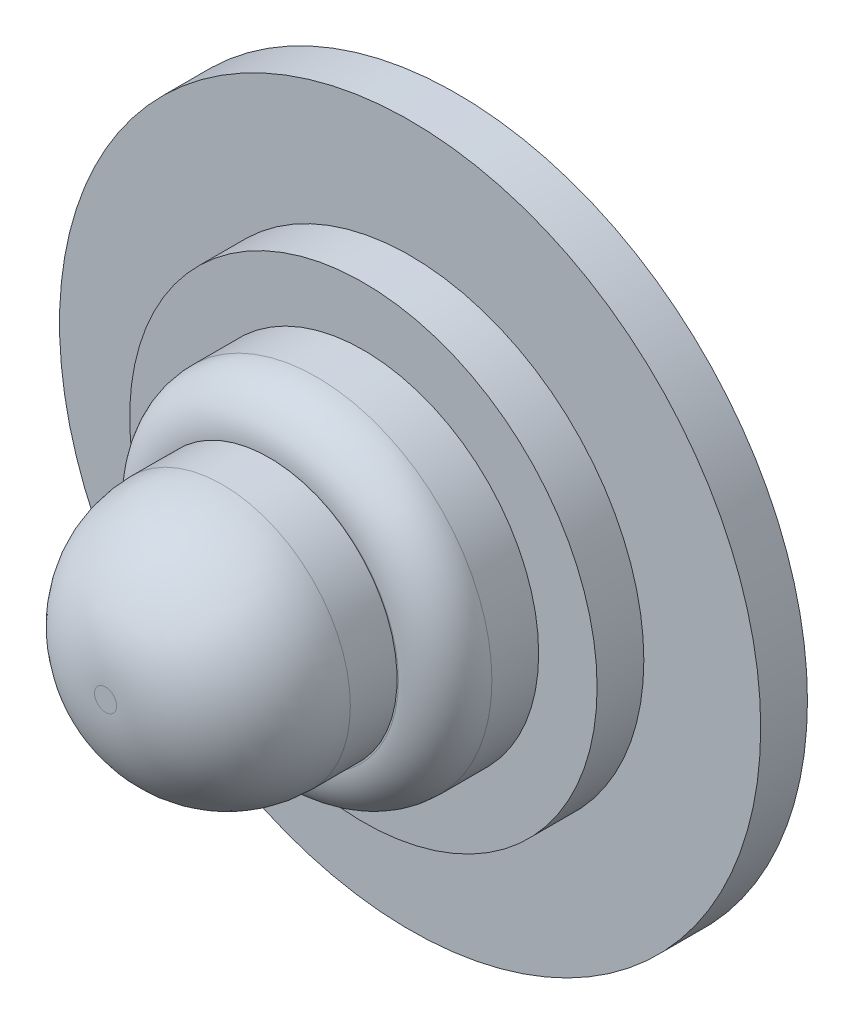
SolidWorks part; units mm, degrees
ref_plane "Front Plane" through (0, 0, 0) normal (0, 0, 1) x (1, 0, 0)
ref_plane "Top Plane" through (0, 0, 0) normal (0, 1, 0) x (1, 0, 0)
ref_plane "Right Plane" through (0, 0, 0) normal (1, 0, 0) x (0, 0, -1)
sketch "Sketch1" plane through (0, 0, 0) normal (0, 0, 1) x (1, 0, 0)
  circle A0 centre (-7.5327, 13.1274) radius 15
  dimension "D1" = 30
extrude "Boss-Extrude1" add sketch "Sketch1" along normal blind 2
sketch "Sketch2" plane through (0, 0, 2) normal (0, 0, 1) x (1, 0, 0)
  circle A0 centre (-7.5327, 13.1274) radius 10
  circle A1 centre (-7.5327, 13.1274) radius 15 construction
  dimension "D1" = 0
  dimension "D2" = 20
extrude "Boss-Extrude2" add sketch "Sketch2" along normal blind 2
sketch "Sketch3" plane through (0, 0, 4) normal (0, 0, 1) x (1, 0, 0)
  circle A0 centre (-7.5327, 13.1274) radius 7.5
  circle A1 centre (-7.5327, 13.1274) radius 10 construction
  dimension "D1" = 0
  dimension "D2" = 15
extrude "Boss-Extrude3" add sketch "Sketch3" along normal blind 4
fillet "Fillet1" radius 2 1 edges at (-0.0327, 13.1274, 8)
sketch "Sketch4" plane through (0, 0, 8) normal (0, 0, 1) x (1, 0, 0)
  circle A0 centre (-7.5617, 13.154) radius 5.4715
extrude "Boss-Extrude4" add sketch "Sketch4" along normal blind 7 contours A0
fillet "Fillet2" radius 5 1 edges at (-2.0901, 13.154, 15)
